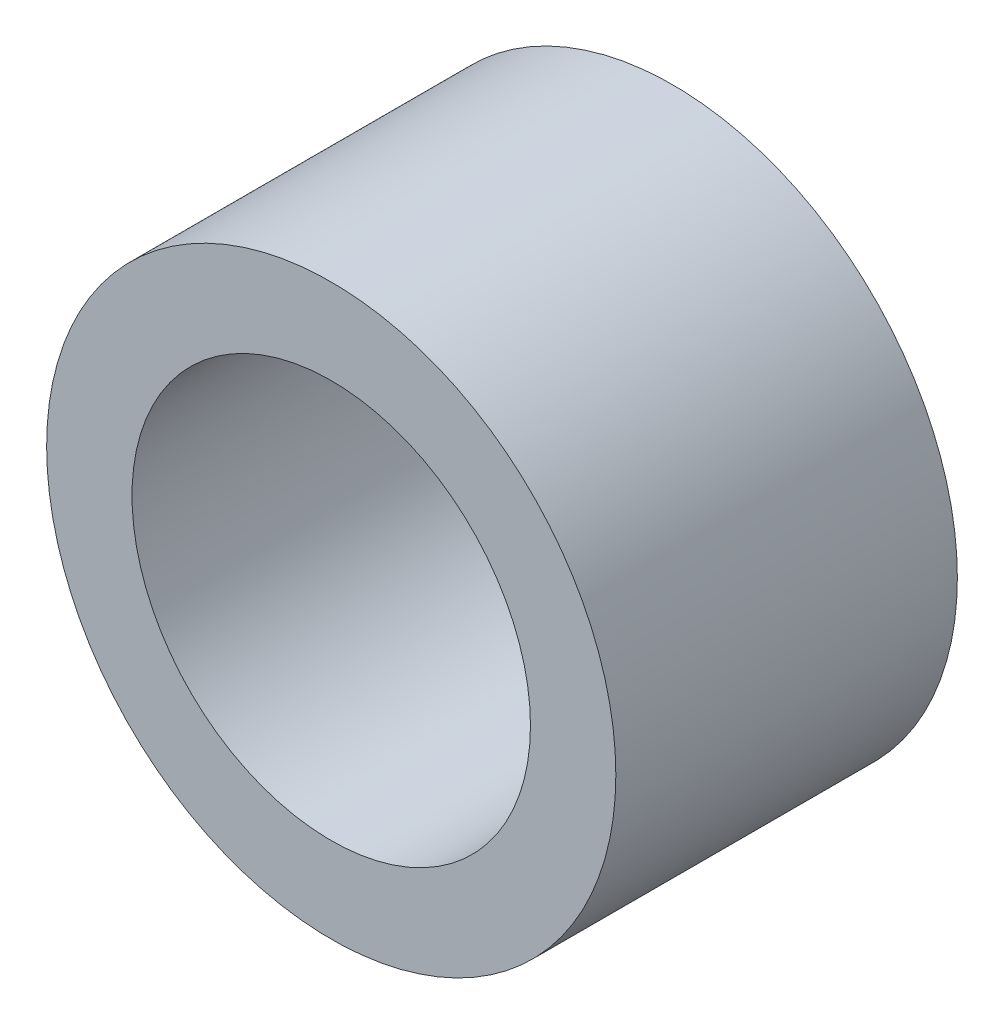
SolidWorks part; units mm, degrees
ref_plane "Plan de face" through (0, 0, 0) normal (0, 0, 1) x (1, 0, 0)
ref_plane "Plan de dessus" through (0, 0, 0) normal (0, 1, 0) x (1, 0, 0)
ref_plane "Plan de droite" through (0, 0, 0) normal (1, 0, 0) x (0, 0, -1)
sketch "Esquisse1" plane through (0, 0, 0) normal (0, 0, 1) x (1, 0, 0)
  circle A0 centre (0, 0) radius 1.75
  circle A1 centre (0, 0) radius 2.5
  point P5 (0, 0)
  dimension "D1" = 3.5
  dimension "D2" = 5
extrude "Boss.-Extru.1" add sketch "Esquisse1" along normal blind 3
